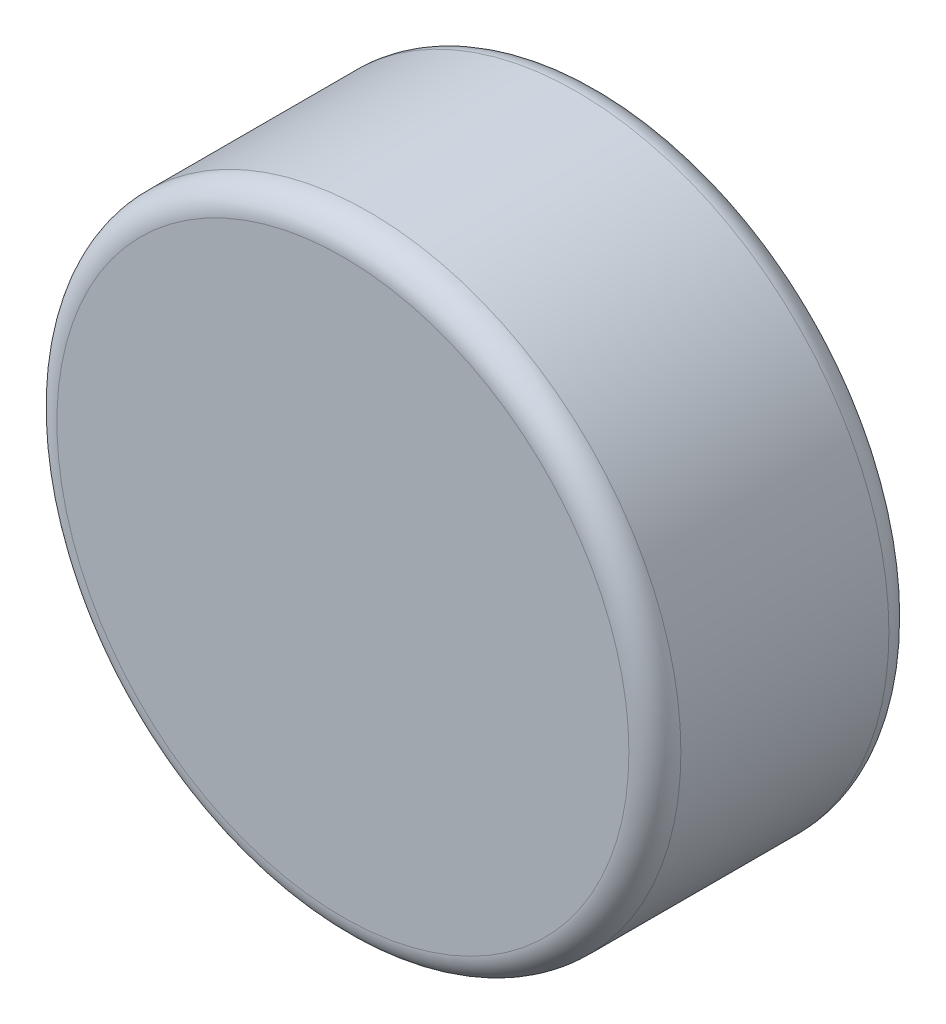
SolidWorks part; units mm, degrees
ref_plane "Front Plane" through (0, 0, 0) normal (0, 0, 1) x (1, 0, 0)
ref_plane "Top Plane" through (0, 0, 0) normal (0, 1, 0) x (1, 0, 0)
ref_plane "Right Plane" through (0, 0, 0) normal (1, 0, 0) x (0, 0, -1)
sketch "Sketch1" plane through (0, 0, 0) normal (0, 0, 1) x (1, 0, 0)
  circle A0 centre (0, 0) radius 3
  dimension "D1" = 6
extrude "Boss-Extrude1" add sketch "Sketch1" along normal blind 2.5
fillet "Fillet1" radius 0.25 2 edges at (3, 0, 0) (3, 0, 2.5)
